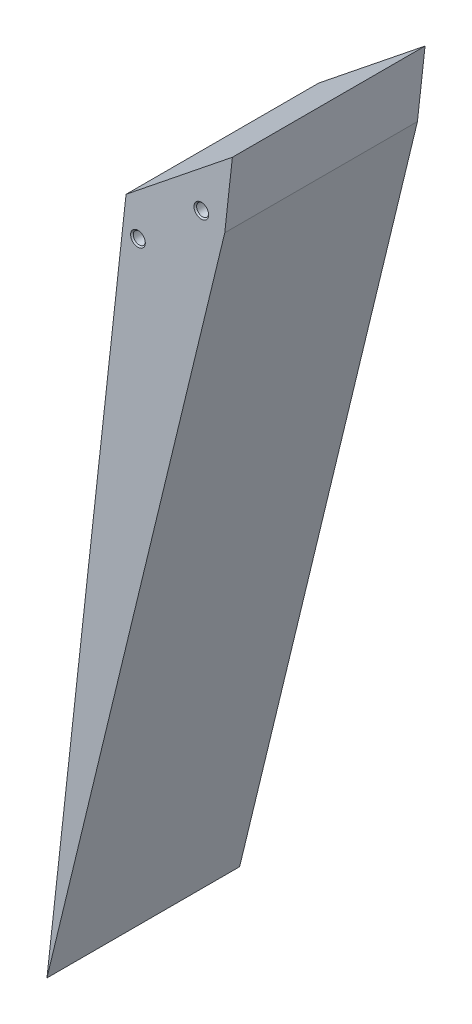
SolidWorks part; units mm, degrees
ref_plane "前视基准面" through (0, 0, 0) normal (0, 0, 1) x (1, 0, 0)
ref_plane "上视基准面" through (0, 0, 0) normal (0, 1, 0) x (1, 0, 0)
ref_plane "右视基准面" through (0, 0, 0) normal (1, 0, 0) x (0, 0, -1)
sketch "草图1" plane through (0, 0, 0) normal (0, 0, 1) x (1, 0, 0)
  line L0 (8.2379, -16.545) -> (-13.8318, -34.2348)
  line L1 (6.6549, -30.9146) -> (9.9399, -1.095) construction
  line L2 (-9.9399, 1.095) -> (-15.4148, -48.6044) construction
  line L3 (-13.8318, -34.2348) -> (-30.2566, -183.3328)
  line L4 (-30.2566, -183.3328) -> (6.6549, -30.9146)
  line L5 (8.2379, -16.545) -> (6.6549, -30.9146)
  line L6 (-15.4148, -48.6044) -> (6.6549, -30.9146) construction
  point P10 (-35.6657, -151.4503)
  point P11 (6.6549, -30.9146)
  dimension "D1" = 150
extrude "凸台-拉伸1" add sketch "草图1" along normal blind 40
sketch "草图6" plane through (0, 0, 40) normal (0, 0, 1) x (1, 0, 0)
  point P0 (-11.358, -41.0029)
  point P3 (1.7945, -29.3731)
hole_wizard "M3 螺纹孔1" positions "草图6" profile "草图5" tap size "M3" standard "GB"
sketch "草图5" plane through (-11.358, -41.0029, 40) normal (1, 0, 0) x (0, -1, 0)
  line L0 (0, 0) -> (0, 8.2511)
  line L1 (0, 8.2511) -> (1.25, 7.5)
  line L2 (1.25, 7.5) -> (1.25, 0.275)
  line L3 (1.25, 0.275) -> (1.525, 0)
  line L5 (1.525, 0) -> (0, 0)
  line L6 (-1.25, 0.275) -> (-1.525, 0) construction
  line L10 (0, 8.2511) -> (-1.25, 7.5) construction
  line L11 (0, -6.35) -> (0, 107.95) construction
  dimension "螺纹孔钻头直径" = 2.5
  dimension "螺纹孔钻头深度" = 7.5
  dimension "近端锥形沉头孔直径" = 3.05
  dimension "近端锥形沉头孔角度" = 90
  dimension "导头角度" = 118
cosmetic thread "孔螺纹线1"
cosmetic thread "孔螺纹线2"
ref_plane "基准面1" through (0, 0, 20) normal (0, 0, 1) x (1, 0, 0)
mirror "镜向1" about plane through (0, 0, 20) normal (0, 0, 1) of "M3 螺纹孔1"
cosmetic thread "孔螺纹线3"
cosmetic thread "孔螺纹线4"
